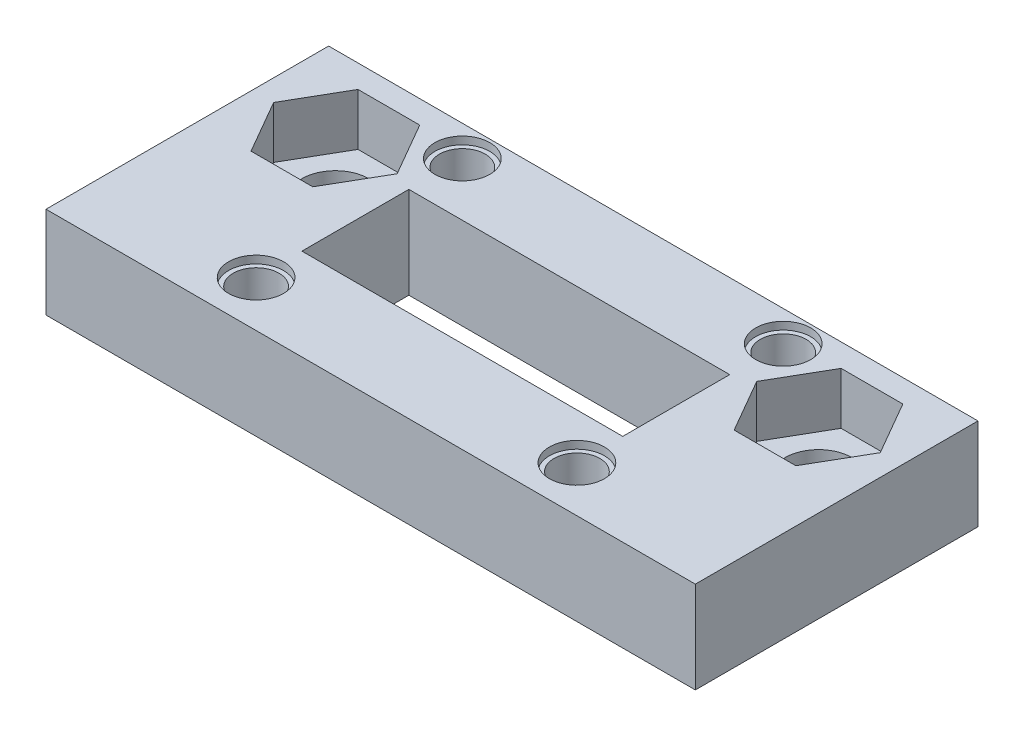
SolidWorks part; units mm, degrees
ref_plane "Front Plane" through (0, 0, 0) normal (0, 0, 1) x (1, 0, 0)
ref_plane "Top Plane" through (0, 0, 0) normal (0, 1, 0) x (1, 0, 0)
ref_plane "Right Plane" through (0, 0, 0) normal (1, 0, 0) x (0, 0, -1)
sketch "Sketch1" plane through (0, 0, 0) normal (0, 1, 0) x (1, 0, 0)
  line L0 (0, 0) -> (21.25, 0)
  line L1 (0, 0) -> (-21.25, 0)
  line L2 (0, 0) -> (0, -2)
  line L3 (0, -2) -> (10.5, -2)
  line L4 (10.5, -2) -> (10.5, -15.5)
  line L5 (10.5, -15.5) -> (-10.5, -15.5)
  line L6 (-10.5, -15.5) -> (-10.5, -2)
  line L7 (-10.5, -2) -> (0, -2)
  line L8 (0, 0) -> (15.81, 0)
  line L9 (15.81, 0) -> (15.81, -5)
  line L10 (0, 0) -> (-15.81, 0)
  line L11 (-15.81, 0) -> (-15.81, -5)
  line L12 (10.5, -15.5) -> (10.5, -18.5)
  line L13 (10.5, -18.5) -> (21.25, -18.5)
  line L14 (21.25, -18.5) -> (21.25, 0)
  line L15 (10.5, -18.5) -> (-21.25, -18.5)
  line L16 (-21.25, 0) -> (-21.25, -18.5)
extrude "Boss-Extrude1" add sketch "Sketch1" along normal blind 8
sketch "Sketch2" plane through (0, 8, 0) normal (0, 1, 0) x (1, 0, 0)
  line L0 (10.5, -15.5) -> (10.5, -18.5) construction
  line L1 (0, 0) -> (21.25, 0) construction
  line L2 (21.25, -18.5) -> (21.25, 0) construction
  line L3 (10.5, -18.5) -> (21.25, -18.5) construction
  line L4 (10.5, -18.5) -> (-21.25, -18.5) construction
  line L5 (-21.25, 0) -> (-21.25, -18.5) construction
  line L6 (0, 0) -> (-21.25, 0) construction
  line L7 (0, 0) -> (-15.81, 0) construction
  line L8 (-15.81, 0) -> (-15.81, -5) construction
  line L9 (0, 0) -> (15.81, 0) construction
  line L10 (15.81, 0) -> (15.81, -5) construction
  line L11 (0, -2) -> (10.5, -2) construction
  line L12 (10.5, -2) -> (10.5, -15.5) construction
  line L13 (10.5, -15.5) -> (-10.5, -15.5) construction
  line L14 (-10.5, -15.5) -> (-10.5, -2) construction
  line L15 (-10.5, -2) -> (0, -2) construction
  line L16 (0, 0) -> (0, -2) construction
  line L17 (10.5, -15.5) -> (10.5, -18.5)
  line L18 (0, 0) -> (21.25, 0)
  line L19 (21.25, -18.5) -> (21.25, 0)
  line L20 (10.5, -18.5) -> (21.25, -18.5)
  line L21 (10.5, -18.5) -> (-21.25, -18.5)
  line L22 (-21.25, 0) -> (-21.25, -18.5)
  line L23 (0, 0) -> (-21.25, 0)
  line L24 (0, 0) -> (-15.81, 0)
  line L25 (-15.81, 0) -> (-15.81, -5)
  line L26 (0, 0) -> (15.81, 0)
  line L27 (15.81, 0) -> (15.81, -5)
  line L28 (0, -2) -> (10.5, -2)
  line L29 (10.5, -2) -> (10.5, -15.5)
  line L30 (10.5, -15.5) -> (-10.5, -15.5)
  line L31 (-10.5, -15.5) -> (-10.5, -2)
  line L32 (-10.5, -2) -> (0, -2)
  line L33 (0, 0) -> (0, -2)
  circle A0 centre (-15.81, -5) radius 2.2
  circle A1 centre (15.81, -5) radius 2.2
extrude "Cut-Extrude1" cut sketch "Sketch2" against normal blind 20
sketch "Sketch3" plane through (0, 8, 0) normal (0, 1, 0) x (1, 0, 0)
  line L0 (10.5, -15.5) -> (10.5, -18.5) construction
  line L1 (0, 0) -> (21.25, 0) construction
  line L2 (21.25, -18.5) -> (21.25, 0) construction
  line L3 (10.5, -18.5) -> (21.25, -18.5) construction
  line L4 (10.5, -18.5) -> (-21.25, -18.5) construction
  line L5 (-21.25, 0) -> (-21.25, -18.5) construction
  line L6 (0, 0) -> (-21.25, 0) construction
  line L7 (0, 0) -> (-15.81, 0) construction
  line L8 (-15.81, 0) -> (-15.81, -5) construction
  line L9 (0, 0) -> (15.81, 0) construction
  line L10 (15.81, 0) -> (15.81, -5) construction
  line L11 (0, -2) -> (10.5, -2) construction
  line L12 (10.5, -2) -> (10.5, -15.5) construction
  line L13 (10.5, -15.5) -> (-10.5, -15.5) construction
  line L14 (-10.5, -15.5) -> (-10.5, -2) construction
  line L15 (-10.5, -2) -> (0, -2) construction
  line L16 (0, 0) -> (0, -2) construction
  line L17 (10.5, -15.5) -> (10.5, -18.5)
  line L18 (0, 0) -> (21.25, 0)
  line L19 (21.25, -18.5) -> (21.25, 0)
  line L20 (10.5, -18.5) -> (21.25, -18.5)
  line L21 (10.5, -18.5) -> (-21.25, -18.5)
  line L22 (-21.25, 0) -> (-21.25, -18.5)
  line L23 (0, 0) -> (-21.25, 0)
  line L24 (0, 0) -> (-15.81, 0)
  line L25 (-15.81, 0) -> (-15.81, -5)
  line L26 (0, 0) -> (15.81, 0)
  line L27 (15.81, 0) -> (15.81, -5)
  line L28 (0, -2) -> (10.5, -2)
  line L29 (10.5, -2) -> (10.5, -15.5)
  line L30 (10.5, -15.5) -> (-10.5, -15.5)
  line L31 (-10.5, -15.5) -> (-10.5, -2)
  line L32 (-10.5, -2) -> (0, -2)
  line L33 (0, 0) -> (0, -2)
  circle A0 centre (-10.5, -2) radius 1.1
  circle A1 centre (10.5, -2) radius 1.1
  circle A2 centre (10.5, -15.5) radius 1.1
  circle A3 centre (-10.5, -15.5) radius 1.1
extrude "Cut-Extrude2" cut sketch "Sketch3" against normal blind 5.3 contours L31 A3 L30 | L30 A3 L31 | L32 A0 L31 | L31 A0 L32 | L28 A1 L29 | L29 A1 L28 | L30 A2 L17 | L17 A2 L29 | L29 A2 L30
sketch "Sketch4" plane through (0, 8, 0) normal (0, 1, 0) x (1, 0, 0)
  circle A0 centre (-10.5, -2) radius 1.5
  circle A1 centre (10.5, -2) radius 1.5
  circle A2 centre (-10.5, -15.5) radius 1.5
  circle A3 centre (10.5, -15.5) radius 1.5
extrude "Cut-Extrude3" cut sketch "Sketch4" against normal blind 4
sketch "Sketch5" plane through (0, 8, 0) normal (0, 1, 0) x (1, 0, 0)
  circle A0 centre (-10.5, -2) radius 1.8
  circle A1 centre (10.5, -2) radius 1.8
  circle A2 centre (-10.5, -15.5) radius 1.8
  circle A3 centre (10.5, -15.5) radius 1.8
extrude "Cut-Extrude4" cut sketch "Sketch5" against normal blind 0.5
sketch "Sketch6" plane through (0, 8, 0) normal (0, 1, 0) x (1, 0, 0)
  line L1 (-11.7685, -5) -> (-13.7893, -1.5)
  line L2 (-13.7893, -1.5) -> (-17.8307, -1.5)
  line L3 (-17.8307, -1.5) -> (-19.8515, -5)
  line L4 (-19.8515, -5) -> (-17.8307, -8.5)
  line L5 (-17.8307, -8.5) -> (-13.7893, -8.5)
  line L6 (-13.7893, -8.5) -> (-11.7685, -5)
  line L7 (19.8515, -5) -> (17.8307, -1.5)
  line L8 (17.8307, -1.5) -> (13.7893, -1.5)
  line L9 (13.7893, -1.5) -> (11.7685, -5)
  line L10 (11.7685, -5) -> (13.7893, -8.5)
  line L11 (13.7893, -8.5) -> (17.8307, -8.5)
  line L12 (17.8307, -8.5) -> (19.8515, -5)
  circle A0 centre (-15.81, -5) radius 3.5 construction
  circle A1 centre (15.81, -5) radius 3.5 construction
extrude "Cut-Extrude5" cut sketch "Sketch6" against normal blind 3.4
sketch "Sketch7" plane through (0, 8, 0) normal (0, 1, 0) x (1, 0, 0)
  line L0 (-10.5, -2) -> (-10.5, -15.5)
  line L1 (-10.5, -15.5) -> (-10.5, -8.75)
  line L2 (-10.5, -8.75) -> (8.8018, -8.75)
  line L3 (10.5, -2) -> (10.5, -9)
  line L4 (10.5, -9) -> (10.5, -5.5)
  line L5 (10.5, -5.5) -> (-10.5, -5.5)
  line L6 (-10.5, -5.5) -> (-10.5, -12.5)
  line L7 (-10.5, -12.5) -> (10.5, -12.5)
  line L8 (10.5, -12.5) -> (10.5, -9)
extrude "Cut-Extrude6" cut sketch "Sketch7" against normal blind 18.4
sketch "Sketch8" plane through (0, 0, 0) normal (0, -1, 0) x (1, 0, 0)
  line L0 (10.5, 15.5) -> (10.5, 18.5) construction
  line L1 (0, 0) -> (21.25, 0) construction
  line L2 (21.25, 18.5) -> (21.25, 0) construction
  line L3 (10.5, 18.5) -> (21.25, 18.5) construction
  line L4 (10.5, 18.5) -> (-21.25, 18.5) construction
  line L5 (-21.25, 0) -> (-21.25, 18.5) construction
  line L6 (0, 0) -> (-21.25, 0) construction
  line L7 (0, 0) -> (-15.81, 0) construction
  line L8 (-15.81, 0) -> (-15.81, 5) construction
  line L9 (0, 0) -> (15.81, 0) construction
  line L10 (15.81, 0) -> (15.81, 5) construction
  line L11 (0, 2) -> (10.5, 2) construction
  line L12 (10.5, 2) -> (10.5, 15.5) construction
  line L13 (10.5, 15.5) -> (-10.5, 15.5) construction
  line L14 (-10.5, 15.5) -> (-10.5, 2) construction
  line L15 (-10.5, 2) -> (0, 2) construction
  line L16 (0, 0) -> (0, 2) construction
  line L17 (10.5, 15.5) -> (10.5, 18.5)
  line L18 (0, 0) -> (21.25, 0)
  line L19 (21.25, 18.5) -> (21.25, 0)
  line L20 (10.5, 18.5) -> (21.25, 18.5)
  line L21 (10.5, 18.5) -> (-21.25, 18.5)
  line L22 (-21.25, 0) -> (-21.25, 18.5)
  line L23 (0, 0) -> (-21.25, 0)
  line L24 (0, 0) -> (-15.81, 0)
  line L25 (-15.81, 0) -> (-15.81, 5)
  line L26 (0, 0) -> (15.81, 0)
  line L27 (15.81, 0) -> (15.81, 5)
  line L28 (0, 2) -> (10.5, 2)
  line L29 (10.5, 2) -> (10.5, 15.5)
  line L30 (10.5, 15.5) -> (-10.5, 15.5)
  line L31 (-10.5, 15.5) -> (-10.5, 2)
  line L32 (-10.5, 2) -> (0, 2)
  line L33 (0, 0) -> (0, 2)
  line L34 (-10.5, 12.5) -> (10.5, 12.5)
  line L35 (10.5, 5.5) -> (-10.5, 5.5)
sketch "Sketch9" plane through (0, 0, 0) normal (0, -1, 0) x (1, 0, 0)
  line L0 (10.5, 15.5) -> (10.5, 18.5) construction
  line L1 (0, 0) -> (21.25, 0) construction
  line L2 (21.25, 18.5) -> (21.25, 0) construction
  line L3 (10.5, 18.5) -> (21.25, 18.5) construction
  line L4 (10.5, 18.5) -> (-21.25, 18.5) construction
  line L5 (-21.25, 0) -> (-21.25, 18.5) construction
  line L6 (0, 0) -> (-21.25, 0) construction
  line L7 (0, 0) -> (-15.81, 0) construction
  line L8 (-15.81, 0) -> (-15.81, 5) construction
  line L9 (0, 0) -> (15.81, 0) construction
  line L10 (15.81, 0) -> (15.81, 5) construction
  line L11 (0, 2) -> (10.5, 2) construction
  line L12 (10.5, 2) -> (10.5, 15.5) construction
  line L13 (10.5, 15.5) -> (-10.5, 15.5) construction
  line L14 (-10.5, 15.5) -> (-10.5, 2) construction
  line L15 (-10.5, 2) -> (0, 2) construction
  line L16 (0, 0) -> (0, 2) construction
  line L17 (10.5, 15.5) -> (10.5, 18.5)
  line L18 (0, 0) -> (21.25, 0)
  line L19 (21.25, 18.5) -> (21.25, 0)
  line L20 (10.5, 18.5) -> (21.25, 18.5)
  line L21 (10.5, 18.5) -> (-21.25, 18.5)
  line L22 (-21.25, 0) -> (-21.25, 18.5)
  line L23 (0, 0) -> (-21.25, 0)
  line L24 (0, 0) -> (-15.81, 0)
  line L25 (-15.81, 0) -> (-15.81, 5)
  line L26 (0, 0) -> (15.81, 0)
  line L27 (15.81, 0) -> (15.81, 5)
  line L28 (0, 2) -> (10.5, 2)
  line L29 (10.5, 2) -> (10.5, 15.5)
  line L30 (10.5, 15.5) -> (-10.5, 15.5)
  line L31 (-10.5, 15.5) -> (-10.5, 2)
  line L32 (-10.5, 2) -> (0, 2)
  line L33 (0, 0) -> (0, 2)
  line L34 (-10.5, 12.5) -> (10.5, 12.5)
  line L35 (10.5, 12.5) -> (10.5, 5.5)
  line L36 (10.5, 5.5) -> (-10.5, 5.5)
  line L37 (-10.5, 5.5) -> (-10.5, 12.5)
extrude "Cut-Extrude8" cut sketch "Sketch9" against normal blind 2
